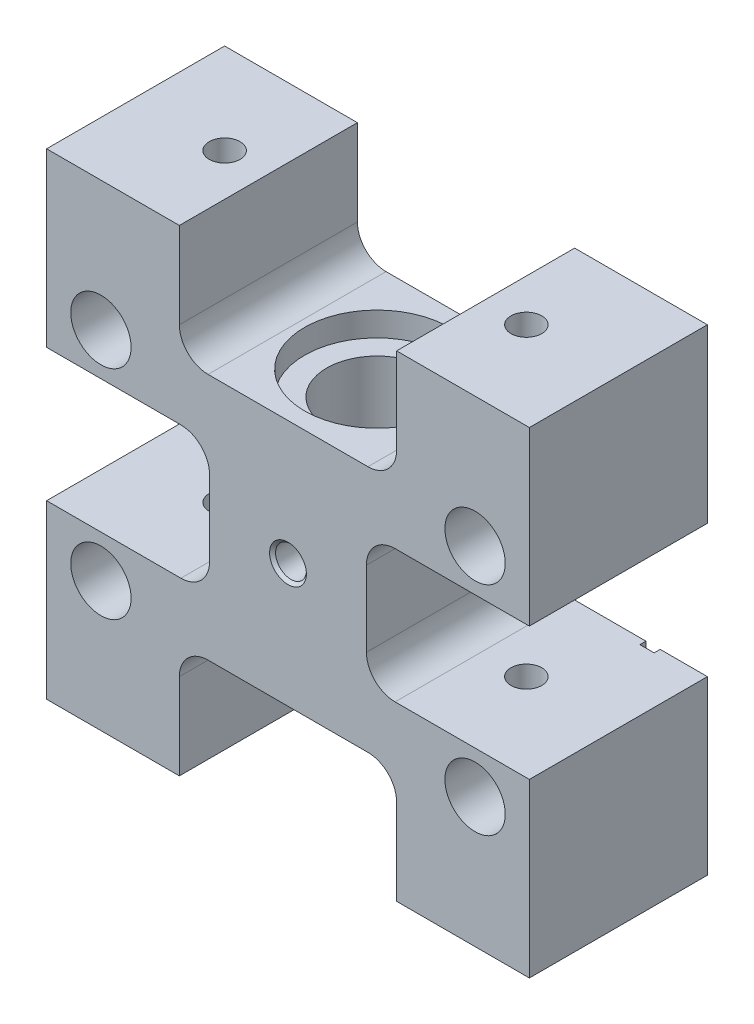
SolidWorks part; units mm, degrees
material "6061-T6 Al"
ref_plane "Front" through (0, 0, 0) normal (0, 0, 1) x (1, 0, 0)
ref_plane "Top" through (0, 0, 0) normal (0, 1, 0) x (1, 0, 0)
ref_plane "Right" through (0, 0, 0) normal (1, 0, 0) x (0, 0, -1)
sketch "Sketch1" plane through (0, 0, 0) normal (0, 0, 1) x (1, 0, 0)
  line L0 (18, 39.5) -> (40, 39.5)
  line L1 (-40, 39.5) -> (-18, 39.5)
  line L2 (-40, 39.5) -> (-40, 11)
  line L3 (-40, -39.5) -> (-18, -39.5)
  line L4 (40, 39.5) -> (40, 11)
  line L5 (-13, 6.25) -> (-13, -6.25)
  line L6 (13, 6.25) -> (13, -6.25)
  line L7 (-17.75, 11) -> (-40, 11)
  line L8 (-17.75, -11) -> (-40, -11)
  line L9 (17.75, 11) -> (40, 11)
  line L10 (17.75, -11) -> (40, -11)
  line L11 (-40, -11) -> (-40, -39.5)
  line L12 (40, -11) -> (40, -39.5)
  line L13 (0, 0) -> (-13, 0) construction
  line L14 (0, 0) -> (13, 0) construction
  line L15 (-13.25, 20.5) -> (13.25, 20.5)
  line L16 (-13.25, -20.5) -> (13.25, -20.5)
  line L17 (-18, 25.25) -> (-18, 39.5)
  line L18 (18, 25.25) -> (18, 39.5)
  line L19 (-18, -25.25) -> (-18, -39.5)
  line L20 (18, -25.25) -> (18, -39.5)
  line L21 (18, -39.5) -> (40, -39.5)
  line L22 (0, 0) -> (0, -20.5) construction
  line L23 (0, 0) -> (0, 20.5) construction
  arc A0 (-18, 25.25) -> (-13.25, 20.5) centre (-13.25, 25.25) ccw
  arc A1 (13.25, 20.5) -> (18, 25.25) centre (13.25, 25.25) ccw
  arc A2 (13, 6.25) -> (17.75, 11) centre (17.75, 6.25) cw
  arc A3 (13, -6.25) -> (17.75, -11) centre (17.75, -6.25) ccw
  arc A4 (13.25, -20.5) -> (18, -25.25) centre (13.25, -25.25) cw
  arc A5 (-18, -25.25) -> (-13.25, -20.5) centre (-13.25, -25.25) cw
  arc A6 (-17.75, -11) -> (-13, -6.25) centre (-17.75, -6.25) ccw
  arc A7 (-17.75, 11) -> (-13, 6.25) centre (-17.75, 6.25) cw
  dimension "D7" = 4.75
  dimension "D1" = 80
  dimension "D2" = 36
  dimension "D3" = 19
  dimension "D4" = 79
  dimension "D5" = 22
  dimension "D6" = 27
extrude "Boss-Extrude1" add sketch "Sketch1" along normal mid plane 29.5
hole_wizard "CBORE for M6 Hex Head Bolt1" positions "Sketch3" profile "Sketch4" counterbore size "M6" standard "Ansi Metric" end condition through all
sketch "Sketch3" plane through (0, 0, 14.75) normal (0, 0, 1) x (1, 0, 0)
  line L0 (-31, 18) -> (31, 18) construction
  line L1 (-31, 18) -> (-31, -18) construction
  line L2 (-31, -18) -> (31, -18) construction
  line L3 (31, -18) -> (31, 18) construction
  line L5 (0, 0) -> (0, 18) construction
  line L6 (0, 0) -> (31, 0) construction
  point P0 (31, 18)
  point P1 (-31, 18)
  point P3 (-31, -18)
  point P5 (31, -18)
  dimension "D1" = 36
  dimension "D2" = 62
sketch "Sketch4" plane through (31, 18, 14.75) normal (1, 0, 0) x (0, -1, 0)
  line L0 (0, 0) -> (0, 29.5)
  line L1 (0, 29.5) -> (3.35, 29.5)
  line L3 (3.35, 29.5) -> (3.35, 16)
  line L4 (3.35, 16) -> (5, 16)
  line L5 (5, 16) -> (5, 0)
  line L7 (5, 0) -> (0, 0)
  line L11 (0, -6.35) -> (0, 107.95) construction
  dimension "Thru Hole Dia." = 6.7
  dimension "Thru Hole Depth" = 29.5
  dimension "C'Bore Dia." = 10
  dimension "C'Bore Depth" = 16
hole_wizard "Tapped Hole for #10-32 Helicoil1" positions "Sketch6" profile "Sketch7" tap size "#10-32" standard "Helicoil® Inch"
sketch "Sketch6" plane through (0, 0, 14.75) normal (0, 0, 1) x (1, 0, 0)
  point P0 (0, 0)
sketch "Sketch7" plane through (0, 0, 14.75) normal (1, 0, 0) x (0, -1, 0)
  line L0 (0, 0) -> (0, 13.5226)
  line L1 (0, 13.5226) -> (2.5527, 11.9888)
  line L2 (2.5527, 11.9888) -> (2.5527, 0.4953)
  line L3 (2.5527, 0.4953) -> (3.048, 0)
  line L5 (3.048, 0) -> (0, 0)
  line L6 (-2.5527, 0.4953) -> (-3.048, 0) construction
  line L10 (0, 13.5226) -> (-2.5527, 11.9888) construction
  line L11 (0, -6.35) -> (0, 107.95) construction
  dimension "Tap Drill Dia." = 5.1054
  dimension "Tap Drill Depth" = 11.9888
  dimension "Near C'Sink Dia." = 6.096
  dimension "Near C'Sink Angle" = 90
  dimension "Drill Angle" = 118
hole_wizard "3/4-10 Tapped Hole1" positions "Sketch9" profile "Sketch10" tap size "3/4-10" standard "Ansi Inch" end condition through all
sketch "Sketch9" plane through (0, 20.5, 0) normal (0, 1, 0) x (-1, 0, 0)
  point P0 (0, 0)
sketch "Sketch10" plane through (0, 20.5, 0) normal (1, 0, 0) x (0, 0, 1)
  line L0 (0, 0) -> (0, 60)
  line L1 (0, 60) -> (8.3337, 60)
  line L2 (8.3337, 60) -> (8.3337, 0)
  line L5 (8.3337, 0) -> (0, 0)
  line L11 (0, -6.35) -> (0, 107.95) construction
  dimension "Thread Major Dia." = 16.6675
  dimension "Thru Tap Drill Depth" = 60
sketch "Sketch11" plane through (0, 20.5, 0) normal (0, 1, 0) x (1, 0, 0)
  circle A0 centre (0, 0) radius 12
  dimension "D1" = 24
extrude "Cut-Extrude1" cut sketch "Sketch11" against normal blind 4
sketch "Sketch12" plane through (0, -20.5, 0) normal (0, -1, 0) x (1, 0, 0)
  circle A0 centre (0, 0) radius 12
  circle A1 centre (0, 0) radius 12 construction
extrude "Cut-Extrude2" cut sketch "Sketch12" against normal blind 4
hole_wizard "1/4-20 Tapped Hole1" positions "Sketch16" profile "Sketch17" tap size "1/4-20" standard "Ansi Inch" end condition up to next
sketch "Sketch16" plane through (0, 39.5, 0) normal (0, 1, 0) x (-1, 0, 0)
  line L0 (25, 0.25) -> (-25, 0.25) construction
  line L1 (0, 0) -> (0, 0.25) construction
  line L2 (-40, -14.75) -> (-18, -14.75) construction
  point P0 (-25, 0.25)
  point P1 (25, 0.25)
  dimension "D1" = 15
  dimension "D2" = 50
sketch "Sketch17" plane through (25, 39.5, 0.25) normal (1, 0, 0) x (0, 0, 1)
  line L0 (0, 0) -> (0, 28.5)
  line L1 (0, 28.5) -> (2.5527, 28.5)
  line L2 (2.5527, 28.5) -> (2.5527, 0)
  line L5 (2.5527, 0) -> (0, 0)
  line L11 (0, -6.35) -> (0, 107.95) construction
  dimension "Thread Major Dia." = 5.1054
  dimension "Thru Tap Drill Depth" = 28.5
hole_wizard "1/4-20 Tapped Hole2" positions "Sketch19" profile "Sketch18" tap size "1/4-20" standard "Ansi Inch" end condition up to next
sketch "Sketch19" plane through (0, -39.5, 0) normal (0, -1, 0) x (1, 0, 0)
  point P0 (25, 0.25)
  point P1 (-25, 0.25)
sketch "Sketch18" plane through (25, -39.5, 0.25) normal (1, 0, 0) x (0, 0, -1)
  line L0 (0, 0) -> (0, 28.5)
  line L1 (0, 28.5) -> (2.5527, 28.5)
  line L2 (2.5527, 28.5) -> (2.5527, 0)
  line L5 (2.5527, 0) -> (0, 0)
  line L11 (0, -6.35) -> (0, 107.95) construction
  dimension "Thread Major Dia." = 5.1054
  dimension "Thru Tap Drill Depth" = 28.5
sketch "Sketch20" plane through (0, 0, -14.75) normal (0, 0, -1) x (-1, 0, 0)
  line L0 (31, 18) -> (31, 15.9177) construction
  line L1 (32.18, -17.6824) -> (29.82, -17.6824)
  line L2 (32.18, -17.6824) -> (32.18, 15.9177)
  line L3 (32.18, 15.9177) -> (29.82, 15.9177)
  line L4 (29.82, -17.6824) -> (29.82, 15.9177)
  line L5 (-29.82, -17.6832) -> (-32.18, -17.6832)
  line L6 (-29.82, -17.6832) -> (-29.82, 15.9177)
  line L7 (-29.82, 15.9177) -> (-32.18, 15.9177)
  line L8 (-32.18, -17.6832) -> (-32.18, 15.9177)
  line L9 (-31, 18) -> (-31, 15.9177) construction
  dimension "D1" = 2.36
  dimension "D2" = 2.36
extrude "Cut-Extrude3" cut sketch "Sketch20" against normal blind 1
